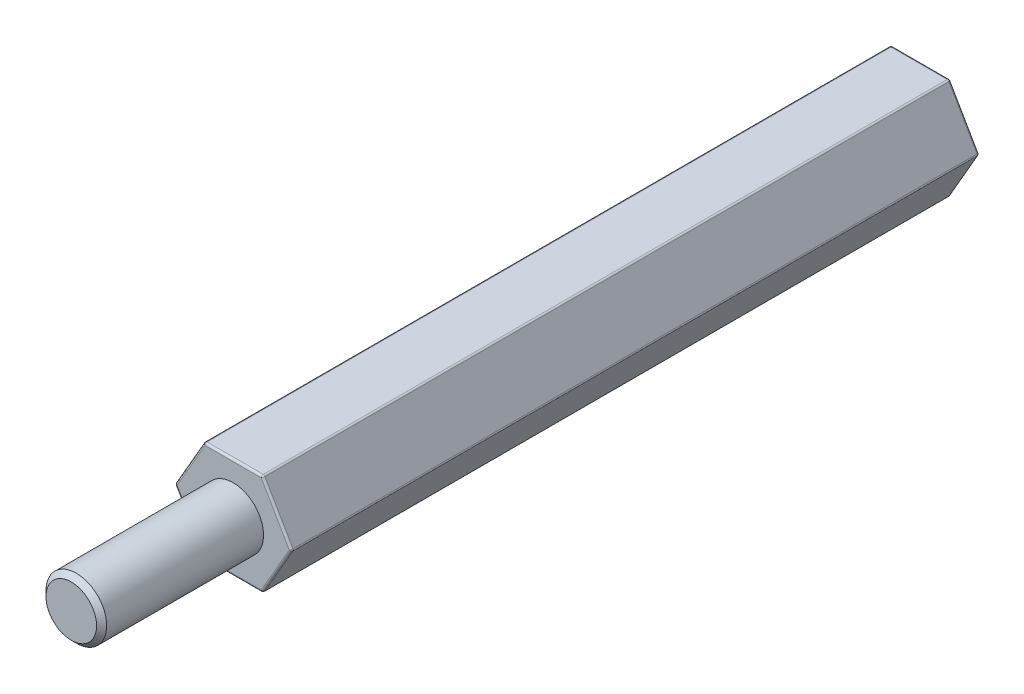
SolidWorks part; units mm, degrees
material "Латунь"
ref_plane "Спереди" through (0, 0, 0) normal (0, 0, 1) x (1, 0, 0)
ref_plane "Сверху" through (0, 0, 0) normal (0, 1, 0) x (1, 0, 0)
ref_plane "Справа" through (0, 0, 0) normal (1, 0, 0) x (0, 0, -1)
sketch "Эскиз1" plane through (0, 0, 0) normal (0, 0, 1) x (1, 0, 0)
  circle A0 centre (0, 0) radius 1.5
  dimension "D1" = 3
extrude "Бобышка-Вытянуть1" add sketch "Эскиз1" along normal blind 8
cosmetic thread "Условное изображение резьбы1" parameters "D1"=2.5
sketch "Эскиз3" plane through (0, 0, 0) normal (0, 0, -1) x (-1, 0, 0)
  line L1 (2.8868, 0) -> (1.4434, 2.5)
  line L2 (1.4434, 2.5) -> (-1.4434, 2.5)
  line L3 (-1.4434, 2.5) -> (-2.8868, 0)
  line L4 (-2.8868, 0) -> (-1.4434, -2.5)
  line L5 (-1.4434, -2.5) -> (1.4434, -2.5)
  line L6 (1.4434, -2.5) -> (2.8868, 0)
  circle A0 centre (0, 0) radius 2.5 construction
  dimension "H1" = 5
extrude "Бобышка-Вытянуть3" add sketch "Эскиз3" along normal blind 34
hole_wizard "Сверление под метчик M3x0.51" positions "Эскиз4" profile "Эскиз5" hole size "M3x0.5" standard "Ansi (метрические)"
sketch "Эскиз4" plane through (0, 0, -34) normal (0, 0, -1) x (-1, 0, 0)
  point P2 (0, 0)
sketch "Эскиз5" plane through (0, 0, -34) normal (1, 0, 0) x (0, 1, 0)
  line L0 (0, 0) -> (0, 5.0511)
  line L1 (0, 5.0511) -> (1.25, 4.3)
  line L2 (1.25, 4.3) -> (1.25, 0)
  line L5 (1.25, 0) -> (0, 0)
  line L10 (0, 5.0511) -> (-1.25, 4.3) construction
  line L11 (0, 0) -> (0, 5.0511) construction
  dimension "P3" = 4.3
  dimension "Угол заточки сверла" = 118
cosmetic thread "Условное изображение резьбы2" parameters "P2"=3, "D2"=3
chamfer "Фаска1" distance 0.25 2 edges at (1.5, 0, 8) (-1.25, 0, -34)
fillet "Скругление1" radius 0.1 18 edges at (0, 2.5, -34) (0, 2.5, 0) (-2.1651, 1.25, -34) (-1.4434, 2.5, -17) (-2.1651, 1.25, 0) (-2.1651, -1.25, -34) (-2.8868, 0, -17) (-2.1651, -1.25, 0) (0, -2.5, -34) (-1.4434, -2.5, -17) (0, -2.5, 0) (2.1651, -1.25, -34) (1.4434, -2.5, -17) (2.1651, -1.25, 0) (1.4434, 2.5, -17) (2.1651, 1.25, -34) (2.8868, 0, -17) (2.1651, 1.25, 0)
